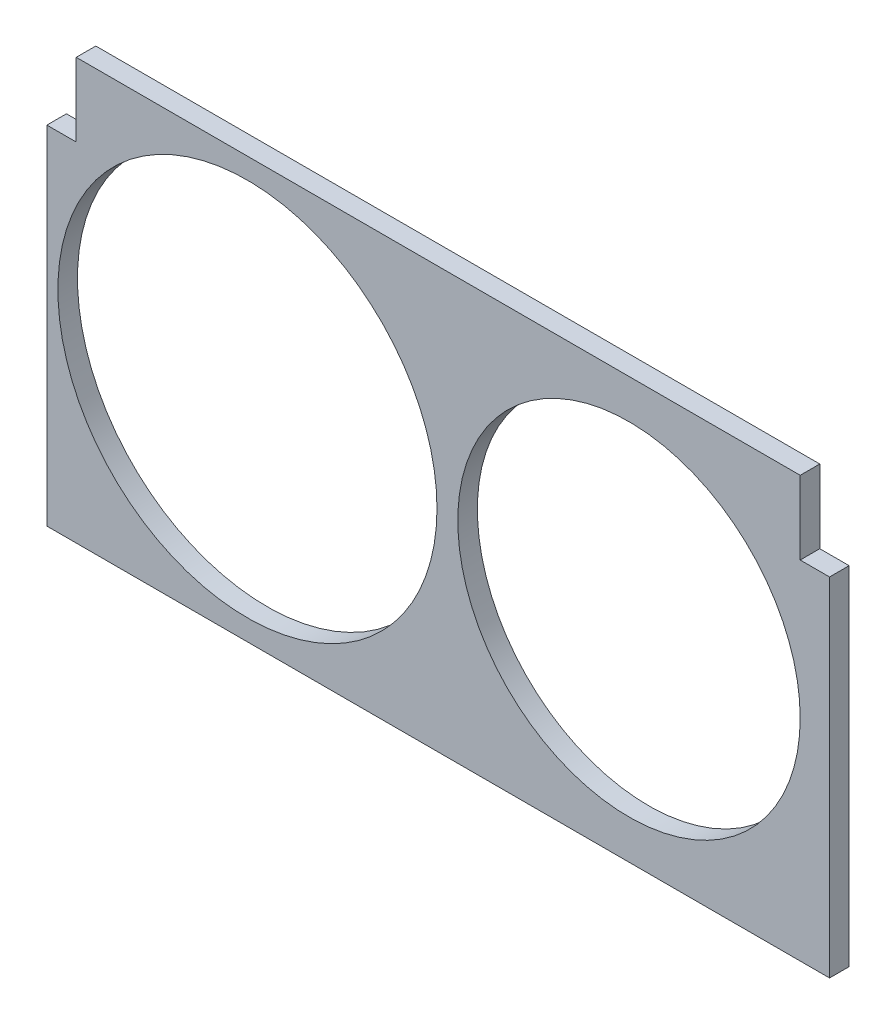
SolidWorks part; units mm, degrees
ref_plane "Front Plane" through (0, 0, 0) normal (0, 0, 1) x (1, 0, 0)
ref_plane "Top Plane" through (0, 0, 0) normal (0, 1, 0) x (1, 0, 0)
ref_plane "Right Plane" through (0, 0, 0) normal (1, 0, 0) x (0, 0, -1)
sketch "Sketch1" plane through (0, 0, 0) normal (0, 0, 1) x (1, 0, 0)
  line L0 (-148.2703, 111.6456) -> (147.7297, 111.6456)
  line L1 (-160.2703, -60.3544) -> (159.7297, -60.3544)
  line L2 (-160.2703, -60.3544) -> (-160.2703, 81.6456)
  line L4 (159.7297, -60.3544) -> (159.7297, 81.6456)
  line L7 (-160.2703, 81.6456) -> (-148.2703, 81.6456)
  line L8 (-148.2703, 111.6456) -> (-148.2703, 81.6456)
  line L11 (159.7297, 81.6456) -> (147.7297, 81.6456)
  line L12 (147.7297, 111.6456) -> (147.7297, 81.6456)
  circle A0 centre (-78.2703, 25.6456) radius 77.5
  circle A1 centre (77.7297, 25.6456) radius 70
  dimension "D3" = 155
  dimension "D4" = 140
  dimension "D1" = 320
  dimension "D2" = 30
  dimension "D5" = 30
  dimension "D6" = 12
  dimension "D7" = 12
  dimension "D8" = 86
  dimension "D9" = 172
  dimension "D10" = 86
  dimension "D11" = 82
  dimension "D12" = 82
extrude "Boss-Extrude1" add sketch "Sketch1" along normal blind 8
sketch "Sketch2" plane through (0, 0, 0) normal (0, 0, 1) x (1, 0, 0)
  line L0 (-0.2703, -60.3544) -> (-0.2703, 111.6456) construction
  line L1 (-160.2703, -60.3544) -> (159.7297, -60.3544) construction
  line L2 (147.7297, 111.6456) -> (-148.2703, 111.6456) construction
  circle A0 centre (-0.2703, 96.6456) radius 1.5
  circle A1 centre (144.7297, -45.3544) radius 1.5
  circle A2 centre (-145.2703, -45.3544) radius 1.5
  dimension "D1" = 3
  dimension "D2" = 3
  dimension "D3" = 3
  dimension "D4" = 15
  dimension "D5" = 15
  dimension "D6" = 15
  dimension "D7" = 15
  dimension "D8" = 15
extrude "Cut-Extrude1" cut sketch "Sketch2" along normal blind 6 from surface at 0 starting at face at (-0.7703, 25.6456, 0)
